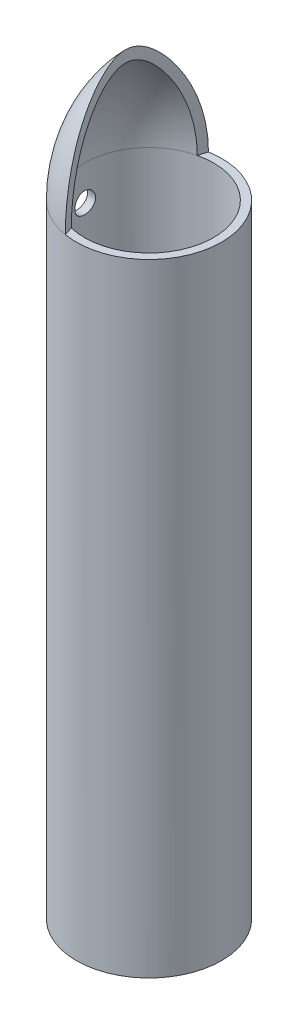
SolidWorks part; units mm, degrees
ref_plane "Front Plane" through (0, 0, 0) normal (0, 0, 1) x (1, 0, 0)
ref_plane "Top Plane" through (0, 0, 0) normal (0, 1, 0) x (1, 0, 0)
ref_plane "Right Plane" through (0, 0, 0) normal (1, 0, 0) x (0, 0, -1)
sketch "Sketch1" plane through (0, 0, 0) normal (0, 1, 0) x (1, 0, 0)
  circle A0 centre (0, 0) radius 9.35
  circle A1 centre (0, 0) radius 10.5
  dimension "D1" = 21
  dimension "D2" = 18.7
extrude "Boss-Extrude1" add sketch "Sketch1" along normal mid plane 90
sketch "Sketch3" plane through (0, 45, 0) normal (0, 1, 0) x (1, 0, 0)
  circle A0 centre (29.75, 0) radius 33.16
  circle A1 centre (0, 0) radius 9.35 construction
  dimension "D1" = 29.75
  dimension "D2" = 66.32
sketch "Sketch2" plane through (0, 0, 0) normal (0, 0, 1) x (1, 0, 0)
  line L0 (0, 65) -> (0, 45) construction
  line L1 (10.5, 45) -> (-10.5, 45) construction
  line L4 (9.35, 45) -> (-9.35, 45) construction
  line L5 (10.5, 45) -> (9.35, 45)
  line L6 (0, 63.586) -> (0, 65)
  arc A0 (10.5, 45) -> (0, 65) centre (-13.7976, 45) ccw
  arc A1 (9.35, 45) -> (0, 63.586) centre (-13.7976, 45) ccw
  dimension "D1" = 20
revolve "Revolve1" add sketch "Sketch2" angle 360 about L0
extrude "Cut-Extrude1" cut sketch "Sketch3" along normal through all contours A0
sketch "Sketch4" plane through (0, 0, 0) normal (1, 0, 0) x (0, 0, -1)
  line L0 (10.5, 45) -> (-10.5, 45) construction
  circle A0 centre (0, 40) radius 1.5
  dimension "D1" = 3
  dimension "D2" = 5
extrude "Cut-Extrude2" cut sketch "Sketch4" against normal through all
